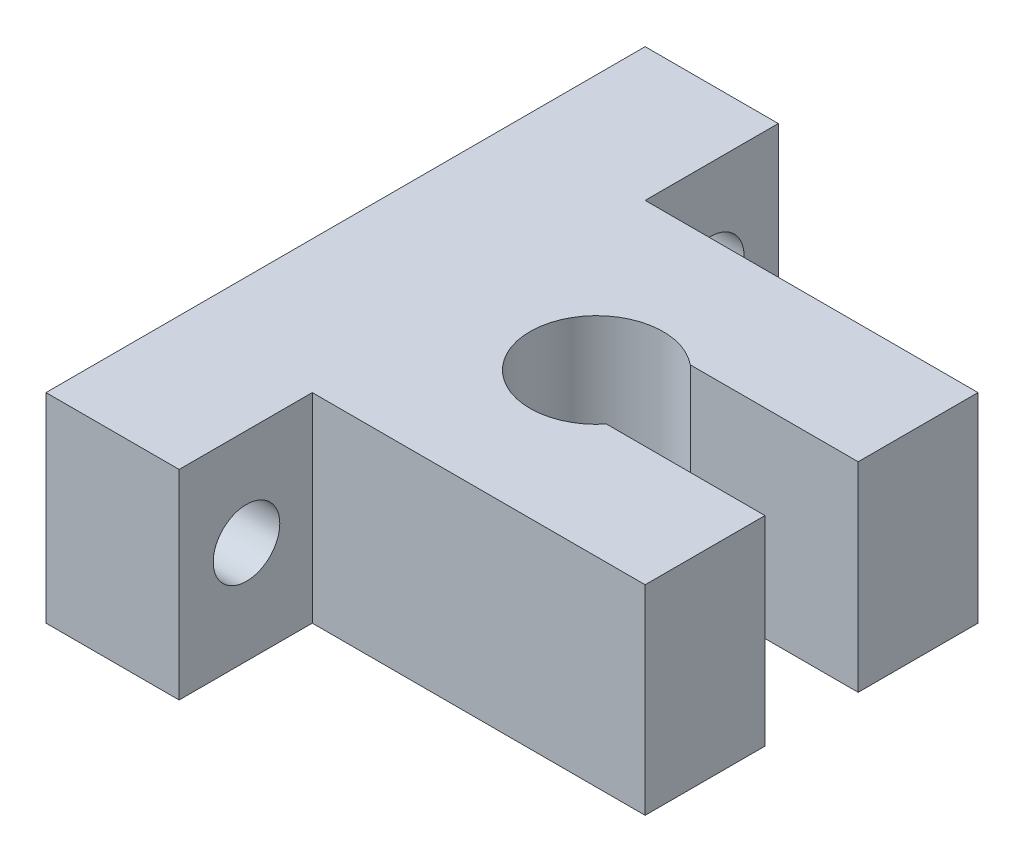
SolidWorks part; units mm, degrees
ref_plane "Front Plane" through (0, 0, 0) normal (0, 0, 1) x (1, 0, 0)
ref_plane "Top Plane" through (0, 0, 0) normal (0, 1, 0) x (1, 0, 0)
ref_plane "Right Plane" through (0, 0, 0) normal (1, 0, 0) x (0, 0, -1)
sketch "Sketch1" plane through (0, 0, 0) normal (0, 1, 0) x (1, 0, 0)
  line L0 (0, 22.8563) -> (0, -22.1437)
  line L1 (0, -22.1437) -> (10, -22.1437)
  line L2 (10, -22.1437) -> (10, -12.1437)
  line L3 (10, -12.1437) -> (35, -12.1437)
  line L4 (35, -12.1437) -> (35, -3.1437)
  line L5 (35, 12.8563) -> (10, 12.8563)
  line L6 (10, 12.8563) -> (10, 22.8563)
  line L7 (10, 22.8563) -> (0, 22.8563)
  line L10 (35, 3.8563) -> (35, 12.8563)
  line L11 (35, 3.8563) -> (22.3897, 3.8563)
  line L12 (35, -3.1437) -> (23.0952, -3.1437)
  arc A1 (22.3897, 3.8563) -> (23.0952, -3.1437) centre (19.2071, 0) ccw
  dimension "D1" = 45
  dimension "D2" = 10
  dimension "D3" = 10
  dimension "D4" = 25
  dimension "D5" = 9
  dimension "D6" = 9
  dimension "D7" = 10
  dimension "D8" = 10
extrude "Boss-Extrude1" add sketch "Sketch1" along normal blind 15
sketch "Sketch5" plane through (10, 0, 0) normal (1, 0, 0) x (0, 0, -1)
  circle A0 centre (-17.0852, 7.6973) radius 2.5
  circle A1 centre (17.7833, 7.6973) radius 2.5
extrude "Cut-Extrude1" cut sketch "Sketch5" against normal blind 10
